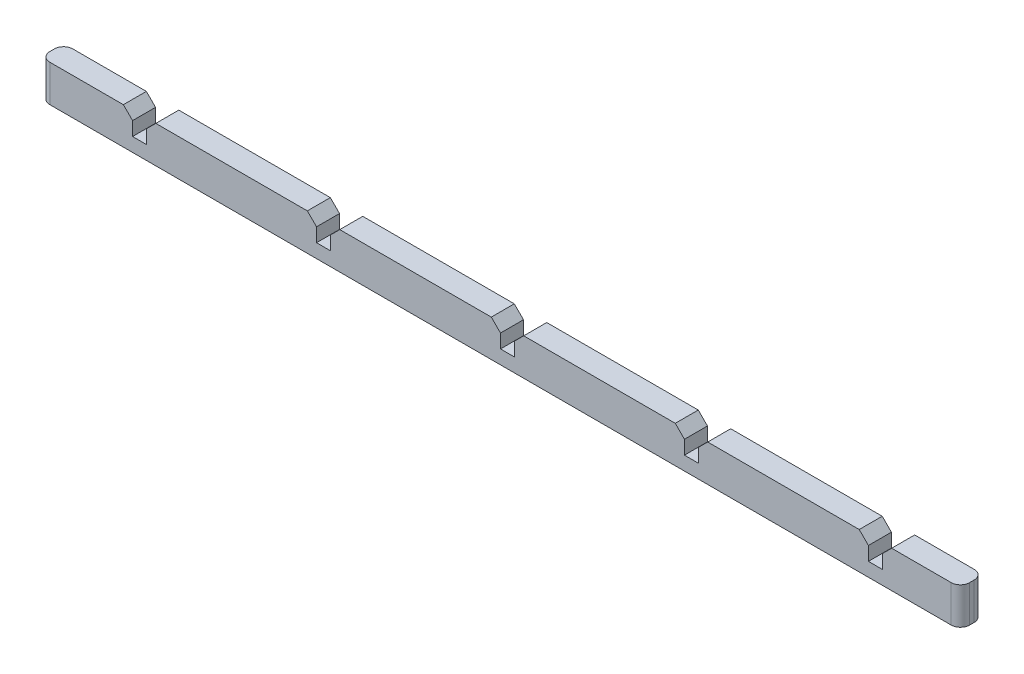
SolidWorks part; units mm, degrees
ref_plane "Front Plane" through (0, 0, 0) normal (0, 0, 1) x (1, 0, 0)
ref_plane "Top Plane" through (0, 0, 0) normal (0, 1, 0) x (1, 0, 0)
ref_plane "Right Plane" through (0, 0, 0) normal (1, 0, 0) x (0, 0, -1)
sketch "Sketch1" plane through (0, 0, 0) normal (0, 1, 0) x (1, 0, 0)
  line L1 (-100, -2.5) -> (100, -2.5)
  line L2 (-100, -2.5) -> (-100, 2.5)
  line L3 (-100, 2.5) -> (100, 2.5)
  line L4 (100, -2.5) -> (100, 2.5)
  line L5 (-100, -2.5) -> (100, 2.5) construction
  line L6 (-100, 2.5) -> (100, -2.5) construction
  point P0 (0, 0)
  dimension "D1" = 5
  dimension "D2" = 200
extrude "Boss-Extrude1" add sketch "Sketch1" along normal blind 8
sketch "Sketch2" plane through (0, 8, 0) normal (0, 1, 0) x (1, 0, 0)
  line L0 (100, 2.5) -> (-100, 2.5) construction
  line L1 (-80, 2.5) -> (-76.95, 2.5)
  line L2 (-80, 2.5) -> (-80, -2.5)
  line L3 (-80, -2.5) -> (-76.95, -2.5)
  line L4 (-76.95, 2.5) -> (-76.95, -2.5)
  line L5 (-100, -2.5) -> (100, -2.5) construction
  line L6 (-100, 2.5) -> (-100, -2.5) construction
  line L7 (-40, 2.5) -> (-40, -2.5)
  line L8 (-40, 2.5) -> (-36.95, 2.5)
  line L9 (-36.95, 2.5) -> (-36.95, -2.5)
  line L10 (-40, -2.5) -> (-36.95, -2.5)
  line L11 (0, 2.5) -> (0, -2.5)
  line L12 (0, 2.5) -> (3.05, 2.5)
  line L13 (3.05, 2.5) -> (3.05, -2.5)
  line L14 (0, -2.5) -> (3.05, -2.5)
  line L15 (40, 2.5) -> (40, -2.5)
  line L16 (40, 2.5) -> (43.05, 2.5)
  line L17 (43.05, 2.5) -> (43.05, -2.5)
  line L18 (40, -2.5) -> (43.05, -2.5)
  line L19 (80, 2.5) -> (80, -2.5)
  line L20 (80, 2.5) -> (83.05, 2.5)
  line L21 (83.05, 2.5) -> (83.05, -2.5)
  line L22 (80, -2.5) -> (83.05, -2.5)
  dimension "D1" = 3.05
  dimension "D2" = 5
  dimension "D3" = 20
  dimension "D4" = 40
extrude "Cut-Extrude1" cut sketch "Sketch2" against normal blind 5
chamfer "Chamfer1" distance 2 angle 45 10 edges at (43.05, 8, 0) (40, 8, 0) (3.05, 8, 0) (0, 8, 0) (-36.95, 8, 0) (-40, 8, 0) (-76.95, 8, 0) (-80, 8, 0) (83.05, 8, 0) (80, 8, 0)
fillet "Fillet1" radius 2 4 edges at (-100, 4, -2.5) (-100, 4, 2.5) (100, 4, -2.5) (100, 4, 2.5)
